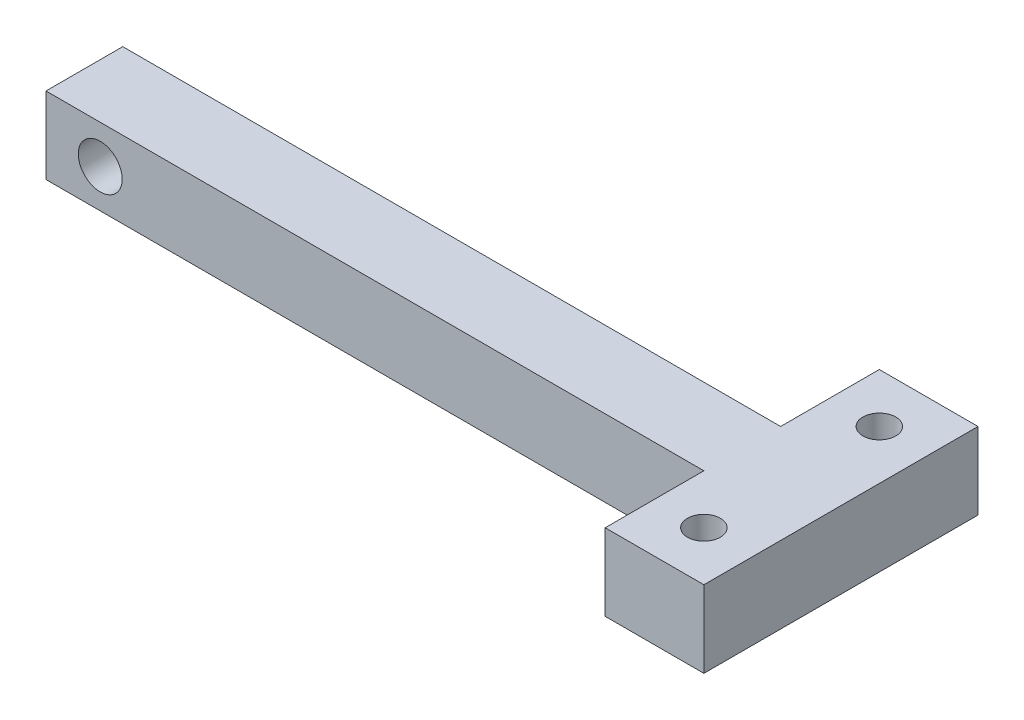
SolidWorks part; units mm, degrees
ref_plane "Front Plane" through (0, 0, 0) normal (0, 0, 1) x (1, 0, 0)
ref_plane "Top Plane" through (0, 0, 0) normal (0, 1, 0) x (1, 0, 0)
ref_plane "Right Plane" through (0, 0, 0) normal (1, 0, 0) x (0, 0, -1)
sketch "Sketch1" plane through (0, 0, 0) normal (0, 1, 0) x (1, 0, 0)
  line L0 (64.5, 16) -> (64.5, -9) construction
  line L1 (0, 0) -> (60, 0)
  line L2 (0, 0) -> (0, 7)
  line L3 (0, 7) -> (60, 7)
  line L4 (60, 0) -> (60, 7)
  line L5 (60, 16) -> (69, 16)
  line L6 (60, 16) -> (60, -9)
  line L7 (60, -9) -> (69, -9)
  line L8 (69, 16) -> (69, -9)
  line L9 (60, 11.5) -> (69, 11.5) construction
  line L10 (60, -4.5) -> (69, -4.5) construction
  circle A0 centre (64.5, 11.5) radius 1.5
  circle A1 centre (64.5, -4.5) radius 1.5
  dimension "D6" = 3
  dimension "D8" = 3
  dimension "D1" = 9
  dimension "D2" = 9
  dimension "D3" = 9
  dimension "D4" = 60
  dimension "D5" = 4.5
  dimension "D7" = 4.5
  dimension "D9" = 7
extrude "Boss-Extrude1" add sketch "Sketch1" along normal blind 7 contours L8 L5 L6 L4 L7 A1 A0 | L1 L4 L3 L2
sketch "Sketch2" plane through (0, 0, -7) normal (0, 0, -1) x (-1, 0, 0)
  line L0 (0, 3.5) -> (-8.8648, 3.5) construction
  line L1 (0, 7) -> (0, 0) construction
  line L2 (-4.945, 7) -> (-4.945, 0) construction
  line L3 (0, 7) -> (-60, 7) construction
  circle A0 centre (-4.945, 3.5) radius 2
  dimension "D1" = 4
extrude "Cut-Extrude1" cut sketch "Sketch2" against normal blind 7
